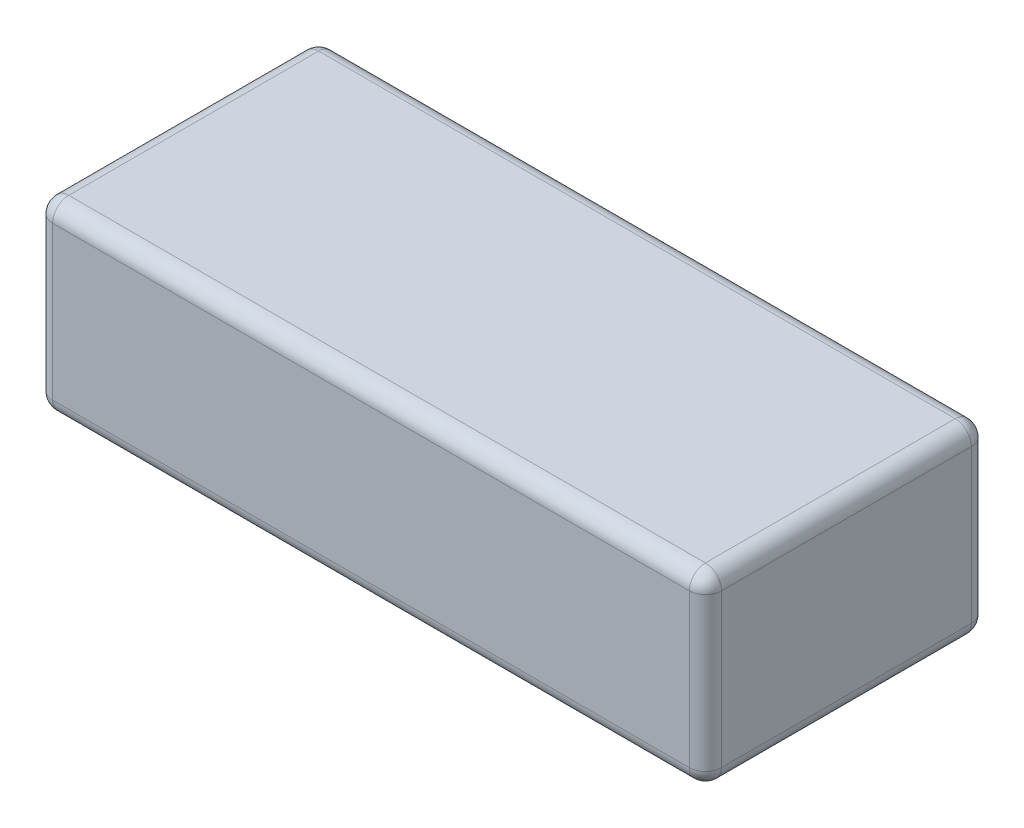
SolidWorks part; units mm, degrees
ref_plane "前视基准面" through (0, 0, 0) normal (0, 0, 1) x (1, 0, 0)
ref_plane "上视基准面" through (0, 0, 0) normal (0, 1, 0) x (1, 0, 0)
ref_plane "右视基准面" through (0, 0, 0) normal (1, 0, 0) x (0, 0, -1)
sketch "草图1" plane through (0, 0, 0) normal (0, 1, 0) x (1, 0, 0)
  line L1 (-41.5, -17.5) -> (41.5, -17.5)
  line L2 (-41.5, -17.5) -> (-41.5, 17.5)
  line L3 (-41.5, 17.5) -> (41.5, 17.5)
  line L4 (41.5, -17.5) -> (41.5, 17.5)
  line L5 (0, 17.5) -> (0, -17.5) construction
  line L6 (-41.5, 0) -> (41.5, 0) construction
  point P0 (0, 0)
  dimension "D1" = 83
  dimension "D2" = 35
extrude "凸台-拉伸1" add sketch "草图1" along normal blind 23
fillet "圆角1" radius 2 12 edges at (41.5, 0, 0) (41.5, 11.5, 17.5) (41.5, 23, 0) (41.5, 11.5, -17.5) (0, 23, -17.5) (0, 0, -17.5) (-41.5, 11.5, -17.5) (-41.5, 0, 0) (-41.5, 23, 0) (-41.5, 11.5, 17.5) (0, 0, 17.5) (0, 23, 17.5)
